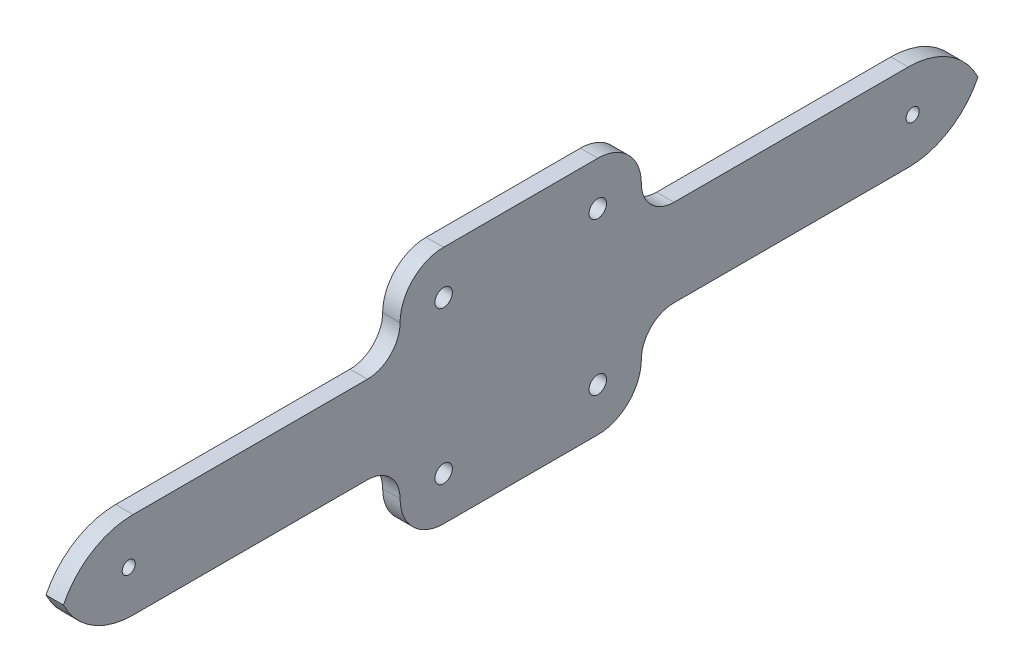
SolidWorks part; units mm, degrees
material "Acrylic (Medium-high impact)"
ref_plane "Front Plane" through (0, 0, 0) normal (0, 0, 1) x (1, 0, 0)
ref_plane "Top Plane" through (0, 0, 0) normal (0, 1, 0) x (1, 0, 0)
ref_plane "Right Plane" through (0, 0, 0) normal (1, 0, 0) x (0, 0, -1)
sketch "Sketch1" plane through (0, 0, 0) normal (1, 0, 0) x (0, 0, -1)
  line L0 (0, 0) -> (-114.2997, 0) construction
  line L1 (105, -30.6352) -> (-105, -30.6352)
  line L2 (105, -30.6352) -> (105, 30.6352)
  line L3 (105, 30.6352) -> (-105, 30.6352)
  line L4 (-105, -30.6352) -> (-105, 30.6352)
  line L5 (105, -30.6352) -> (-105, 30.6352) construction
  line L6 (105, 30.6352) -> (-105, -30.6352) construction
  point P0 (0, 0)
  dimension "D1" = 210
extrude "Boss-Extrude1" add sketch "Sketch1" along normal blind 4
sketch "Sketch2" plane through (4, 0, 0) normal (1, 0, 0) x (0, 0, -1)
  circle A2 centre (-90, 0) radius 1.5
  dimension "D1" = 3
  dimension "D2" = 90
extrude "Cut-Extrude1" cut sketch "Sketch2" against normal through all
sketch "Sketch3" plane through (4, 0, 0) normal (1, 0, 0) x (0, 0, -1)
  line L0 (0, 55) -> (0, -55) construction
  line L1 (55, 0) -> (-55, 0) construction
  circle A0 centre (-17.7, 17.5) radius 2
  dimension "D1" = 4
  dimension "D2" = 17.7
  dimension "D3" = 17.5
extrude "Cut-Extrude2" cut sketch "Sketch3" against normal through all
sketch "Sketch4" plane through (4, 0, 0) normal (1, 0, 0) x (0, 0, -1)
  line L0 (-89, 10) -> (-35.2, 10)
  line L2 (-105, 0) -> (-105, 30.6352)
  line L5 (-105, 30.6352) -> (0, 30.6352)
  line L6 (105, 30.6352) -> (-105, 30.6352) construction
  line L8 (-17.7, 27.5) -> (0, 27.5)
  line L9 (2.2, 0) -> (-2.2, 0) construction
  line L11 (0, 27.5) -> (0, 30.6352)
  line L12 (-105, 30.6352) -> (-105, -30.6352) construction
  arc A7 (-17.7, 27.5) -> (-27.7, 17.5) centre (-17.7, 17.5) ccw
  arc A13 (-35.2, 10) -> (-27.7, 17.5) centre (-35.2, 17.5) ccw
  arc A18 (-105, 0) -> (-89, 10) centre (-89, -7.8) cw
  circle A19 centre (-90, 0) radius 1.5 construction
  dimension "D1" = 16
  dimension "D2" = 20
  dimension "D3" = 10
  dimension "D4" = 0
extrude "Cut-Extrude3" cut sketch "Sketch4" against normal through all
mirror "Mirror2" about plane through (0, 0, 0) normal (0, 1, 0) of "Cut-Extrude3", "Cut-Extrude2"
mirror "Mirror3" about plane through (0, 0, 0) normal (0, 0, 1) of "Mirror2", "Cut-Extrude3", "Cut-Extrude1", "Cut-Extrude2"
